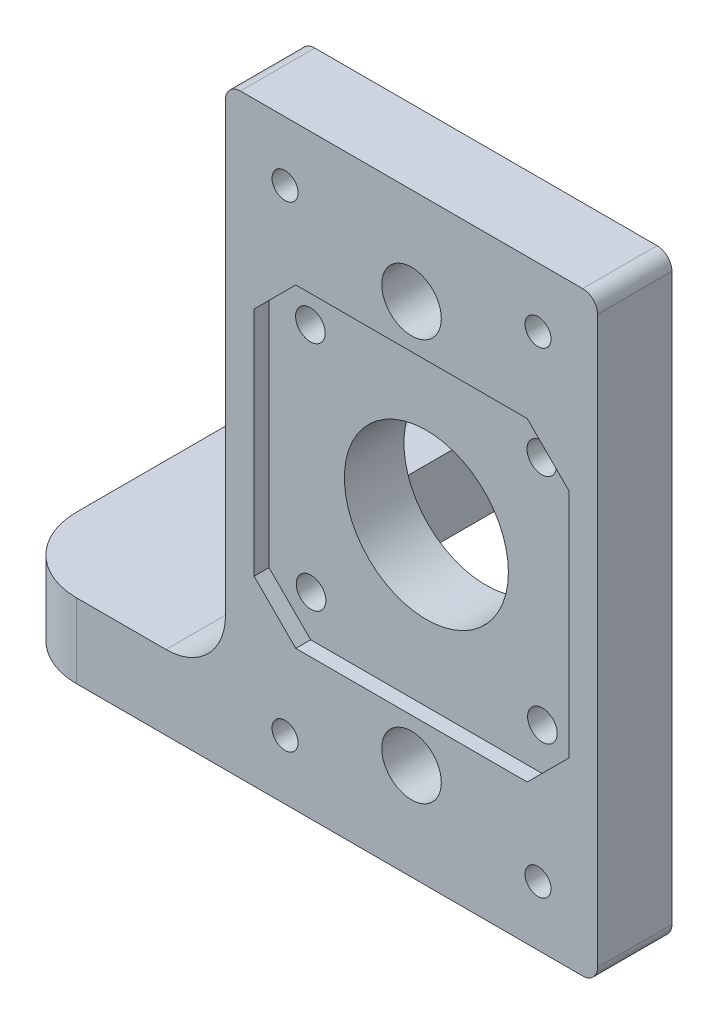
SolidWorks part; units mm, degrees
ref_plane "Plano frontal" through (0, 0, 0) normal (0, 0, 1) x (1, 0, 0)
ref_plane "Plano superior" through (0, 0, 0) normal (0, 1, 0) x (1, 0, 0)
ref_plane "Plano direito" through (0, 0, 0) normal (1, 0, 0) x (0, 0, -1)
sketch "Esboço1" plane through (0, 0, 0) normal (0, 0, 1) x (1, 0, 0)
  line L1 (-25, 40) -> (25, 40)
  line L2 (-25, 40) -> (-25, -40)
  line L3 (-25, -40) -> (25, -40)
  line L4 (25, 40) -> (25, -40)
  line L5 (-25, 40) -> (25, -40) construction
  line L6 (-25, -40) -> (25, 40) construction
  point P0 (0, 0)
  dimension "D1" = 80
  dimension "D2" = 50
extrude "Ressalto-extrusão1" add sketch "Esboço1" along normal mid plane 10
sketch "Esboço2" plane through (0, 0, 5) normal (0, 0, 1) x (1, 0, 0)
  line L1 (-21.15, 21.15) -> (21.15, 21.15)
  line L2 (-21.15, 21.15) -> (-21.15, -21.15)
  line L3 (-21.15, -21.15) -> (21.15, -21.15)
  line L4 (21.15, 21.15) -> (21.15, -21.15)
  line L5 (-21.15, 21.15) -> (21.15, -21.15) construction
  line L6 (-21.15, -21.15) -> (21.15, 21.15) construction
  point P0 (0, 0)
  dimension "D1" = 42.3
  dimension "D2" = 42.3
extrude "Corte-extrusão1" cut sketch "Esboço2" against normal blind 2
sketch "Esboço3" plane through (0, 0, 3) normal (0, 0, 1) x (1, 0, 0)
  circle A0 centre (0, 0) radius 11.02
  dimension "D1" = 22.04
extrude "Corte-extrusão2" cut sketch "Esboço3" against normal blind 24
sketch "Esboço4" plane through (0, 0, 3) normal (0, 0, 1) x (1, 0, 0)
  line L1 (-21.15, 21.15) -> (-21.15, -21.15) construction
  line L2 (21.15, 21.15) -> (-21.15, 21.15) construction
  circle A0 centre (-15.59, 15.5) radius 1.9879
  dimension "D2" = 5.65
  dimension "D1" = 5.56
extrude "Corte-extrusão3" cut sketch "Esboço4" against normal blind 24
pattern_circular "PadrãoCircular1" count 4 over 360 about axis through (0, 0, 0) along (0, 0, 1) of "Corte-extrusão3"
sketch "Esboço5" plane through (0, 0, 5) normal (0, 0, 1) x (1, 0, 0)
  circle A0 centre (0, 27) radius 4
  circle A1 centre (0, -27) radius 4
  circle A2 centre (0, 0) radius 11.02 construction
  dimension "D1" = 27
  dimension "D2" = 27
  dimension "D3" = 8
  dimension "D4" = 8
extrude "Corte-extrusão4" cut sketch "Esboço5" against normal blind 24
chamfer "Chanfro1" distance 5.6 4 edges at (-21.15, 21.15, 4) (21.15, 21.15, 4) (21.15, -21.15, 4) (-21.15, -21.15, 4)
sketch "Esboço6" plane through (0, 0, -5) normal (0, 0, -1) x (-1, 0, 0)
  line L0 (-25, 40) -> (25, 40) construction
  line L1 (-25, -40) -> (-25, 40) construction
  line L2 (25, 40) -> (25, -40) construction
  line L3 (25, -40) -> (-25, -40) construction
  circle A0 centre (-17, 32) radius 1.75
  circle A1 centre (17, 32) radius 1.75
  circle A2 centre (-17, -32) radius 1.75
  circle A3 centre (17, -32) radius 1.75
  dimension "D1" = 3.5
  dimension "D2" = 3.5
  dimension "D3" = 3.5
  dimension "D4" = 3.5
  dimension "D5" = 8
  dimension "D6" = 8
  dimension "D7" = 8
  dimension "D8" = 8
  dimension "D9" = 8
  dimension "D10" = 8
  dimension "D11" = 8
  dimension "D12" = 8
extrude "Corte-extrusão5" cut sketch "Esboço6" against normal blind 10
fillet "Filete1" radius 2 3 edges at (25, 40, 0) (-25, 40, 0) (25, -40, 0)
sketch "Esboço7" plane through (0, 0, -5) normal (0, 0, -1) x (-1, 0, 0)
  line L1 (25, -40) -> (55, -40)
  line L2 (25, -40) -> (25, -30)
  line L3 (25, -30) -> (55, -30)
  line L4 (55, -40) -> (55, -30)
  dimension "D1" = 30
  dimension "D2" = 10
extrude "Ressalto-extrusão2" add sketch "Esboço7" along normal blind 50 and the other way blind 10
sketch "Esboço8" plane through (0, -40, 0) normal (0, -1, 0) x (-1, 0, 0)
  line L0 (25, 5) -> (-23, 5) construction
  line L1 (25, 5) -> (25, 55) construction
  circle A0 centre (46, 45.5) radius 4.05
  dimension "D1" = 8.1
  dimension "D2" = 40.5
  dimension "D3" = 21
extrude "Corte-extrusão6" cut sketch "Esboço8" against normal blind 45
sketch "Esboço9" plane through (0, -40, 0) normal (0, -1, 0) x (-1, 0, 0)
  line L0 (25, 55) -> (55, 55) construction
  line L1 (25, 5) -> (37, 5)
  line L2 (25, 5) -> (25, 55)
  line L3 (25, 55) -> (37, 55)
  line L4 (37, 5) -> (37, 55)
  circle A0 centre (46, 45.5) radius 4.05 construction
  dimension "D1" = 9
extrude "Corte-extrusão7" cut sketch "Esboço9" against normal blind 45
fillet "Filete2" radius 10 2 edges at (-55, -35, 5) (-37, -35, -5)
fillet "Filete3" radius 8 1 edges at (-25, -30, 0)
